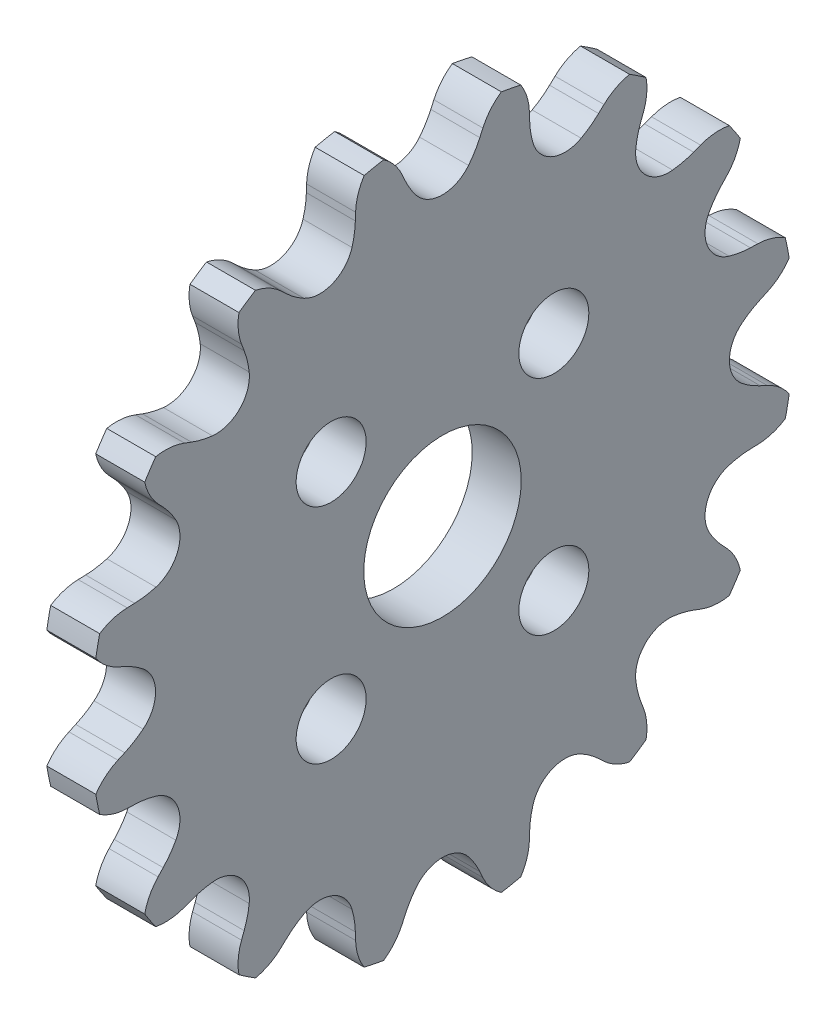
SolidWorks part; units mm, degrees
ref_plane "Front Plane" through (0, 0, 0) normal (0, 0, 1) x (1, 0, 0)
ref_plane "Top Plane" through (0, 0, 0) normal (0, 1, 0) x (1, 0, 0)
ref_plane "Right Plane" through (0, 0, 0) normal (1, 0, 0) x (0, 0, -1)
ref_plane "Plane1" through (0, 0, 0) normal (-1, 0, 0) x (0, -1, 0)
sketch "Sketch1" plane through (0, 0, 0) normal (-1, 0, 0) x (0, -1, 0)
  line L0 (-15.6424, 4.4271) -> (-16.0207, 4.4156)
  line L1 (-16.491, 2.0514) -> (-16.1459, 1.896)
  line L2 (-16.1459, -1.896) -> (-16.491, -2.0514)
  line L3 (-16.0207, -4.4156) -> (-15.6424, -4.4271)
  line L4 (-14.1913, -7.9304) -> (-14.4506, -8.2061)
  line L5 (-13.1114, -10.2103) -> (-12.7575, -10.0762)
  line L6 (-10.0762, -12.7575) -> (-10.2103, -13.1114)
  line L7 (-8.2061, -14.4506) -> (-7.9304, -14.1913)
  line L8 (-4.4271, -15.6424) -> (-4.4156, -16.0207)
  line L9 (-2.0514, -16.491) -> (-1.896, -16.1459)
  line L10 (1.896, -16.1459) -> (2.0514, -16.491)
  line L11 (4.4156, -16.0207) -> (4.4271, -15.6424)
  line L12 (7.9304, -14.1913) -> (8.2061, -14.4506)
  line L13 (10.2103, -13.1114) -> (10.0762, -12.7575)
  line L14 (12.7575, -10.0762) -> (13.1114, -10.2103)
  line L15 (14.4506, -8.2061) -> (14.1913, -7.9304)
  line L16 (15.6424, -4.4271) -> (16.0207, -4.4156)
  line L17 (16.491, -2.0514) -> (16.1459, -1.896)
  line L18 (16.1459, 1.896) -> (16.491, 2.0514)
  line L19 (16.0207, 4.4156) -> (15.6424, 4.4271)
  line L20 (14.1913, 7.9304) -> (14.4506, 8.2061)
  line L21 (13.1114, 10.2103) -> (12.7575, 10.0762)
  line L22 (10.0762, 12.7575) -> (10.2103, 13.1114)
  line L23 (8.2061, 14.4506) -> (7.9304, 14.1913)
  line L24 (4.4271, 15.6424) -> (4.4156, 16.0207)
  line L25 (2.0514, 16.491) -> (1.896, 16.1459)
  line L26 (-1.896, 16.1459) -> (-2.0514, 16.491)
  line L27 (-4.4156, 16.0207) -> (-4.4271, 15.6424)
  line L28 (-7.9304, 14.1913) -> (-8.2061, 14.4506)
  line L29 (-10.2103, 13.1114) -> (-10.0762, 12.7575)
  line L30 (-12.7575, 10.0762) -> (-13.1114, 10.2103)
  line L31 (-14.4506, 8.2061) -> (-14.1913, 7.9304)
  arc A0 (-13.5476, 7.0444) -> (-14.5607, 4.5984) centre (-15.0357, 6.228) cw
  arc A1 (-14.5607, 4.5984) -> (-15.6424, 4.4271) centre (-15.7749, 8.7641) cw
  arc A2 (-16.0207, 4.4156) -> (-17.4181, 3.9791) centre (-15.9376, 1.694) ccw
  arc A3 (-17.4181, 3.9791) -> (-17.6149, 2.9894) centre (0, 0) ccw
  arc A4 (-17.6149, 2.9894) -> (-16.491, 2.0514) centre (-15.3726, 4.534) ccw
  arc A5 (-16.1459, 1.896) -> (-15.2121, 1.3237) centre (-17.928, -2.0601) cw
  arc A6 (-15.2121, 1.3237) -> (-15.2121, -1.3237) centre (-16.2745, 0) cw
  arc A7 (-15.2121, -1.3237) -> (-16.1459, -1.896) centre (-17.928, 2.0601) cw
  arc A8 (-16.491, -2.0514) -> (-17.6149, -2.9894) centre (-15.3726, -4.534) ccw
  arc A9 (-17.6149, -2.9894) -> (-17.4181, -3.9791) centre (0, 0) ccw
  arc A10 (-17.4181, -3.9791) -> (-16.0207, -4.4156) centre (-15.9376, -1.694) ccw
  arc A11 (-15.6424, -4.4271) -> (-14.5607, -4.5984) centre (-15.7749, -8.7641) cw
  arc A12 (-14.5607, -4.5984) -> (-13.5476, -7.0444) centre (-15.0357, -6.228) cw
  arc A13 (-13.5476, -7.0444) -> (-14.1913, -7.9304) centre (-17.3517, -4.9574) cw
  arc A14 (-14.4506, -8.2061) -> (-15.1301, -9.5028) centre (-12.4674, -10.0717) ccw
  arc A15 (-15.1301, -9.5028) -> (-14.5694, -10.3419) centre (0, 0) ccw
  arc A16 (-14.5694, -10.3419) -> (-13.1114, -10.2103) centre (-14.0761, -7.6641) ccw
  arc A17 (-12.7575, -10.0762) -> (-11.6926, -9.8206) centre (-11.2202, -14.1337) cw
  arc A18 (-11.6926, -9.8206) -> (-9.8206, -11.6926) centre (-11.5078, -11.5078) cw
  arc A19 (-9.8206, -11.6926) -> (-10.0762, -12.7575) centre (-14.1337, -11.2202) cw
  arc A20 (-10.2103, -13.1114) -> (-10.3419, -14.5694) centre (-7.6641, -14.0761) ccw
  arc A21 (-10.3419, -14.5694) -> (-9.5028, -15.1301) centre (0, 0) ccw
  arc A22 (-9.5028, -15.1301) -> (-8.2061, -14.4506) centre (-10.0717, -12.4674) ccw
  arc A23 (-7.9304, -14.1913) -> (-7.0444, -13.5476) centre (-4.9574, -17.3517) cw
  arc A24 (-7.0444, -13.5476) -> (-4.5984, -14.5607) centre (-6.228, -15.0357) cw
  arc A25 (-4.5984, -14.5607) -> (-4.4271, -15.6424) centre (-8.7641, -15.7749) cw
  arc A26 (-4.4156, -16.0207) -> (-3.9791, -17.4181) centre (-1.694, -15.9376) ccw
  arc A27 (-3.9791, -17.4181) -> (-2.9894, -17.6149) centre (0, 0) ccw
  arc A28 (-2.9894, -17.6149) -> (-2.0514, -16.491) centre (-4.534, -15.3726) ccw
  arc A29 (-1.896, -16.1459) -> (-1.3237, -15.2121) centre (2.0601, -17.928) cw
  arc A30 (-1.3237, -15.2121) -> (1.3237, -15.2121) centre (0, -16.2745) cw
  arc A31 (1.3237, -15.2121) -> (1.896, -16.1459) centre (-2.0601, -17.928) cw
  arc A32 (2.0514, -16.491) -> (2.9894, -17.6149) centre (4.534, -15.3726) ccw
  arc A33 (2.9894, -17.6149) -> (3.9791, -17.4181) centre (0, 0) ccw
  arc A34 (3.9791, -17.4181) -> (4.4156, -16.0207) centre (1.694, -15.9376) ccw
  arc A35 (4.4271, -15.6424) -> (4.5984, -14.5607) centre (8.7641, -15.7749) cw
  arc A36 (4.5984, -14.5607) -> (7.0444, -13.5476) centre (6.228, -15.0357) cw
  arc A37 (7.0444, -13.5476) -> (7.9304, -14.1913) centre (4.9574, -17.3517) cw
  arc A38 (8.2061, -14.4506) -> (9.5028, -15.1301) centre (10.0717, -12.4674) ccw
  arc A39 (9.5028, -15.1301) -> (10.3419, -14.5694) centre (0, 0) ccw
  arc A40 (10.3419, -14.5694) -> (10.2103, -13.1114) centre (7.6641, -14.0761) ccw
  arc A41 (10.0762, -12.7575) -> (9.8206, -11.6926) centre (14.1337, -11.2202) cw
  arc A42 (9.8206, -11.6926) -> (11.6926, -9.8206) centre (11.5078, -11.5078) cw
  arc A43 (11.6926, -9.8206) -> (12.7575, -10.0762) centre (11.2202, -14.1337) cw
  arc A44 (13.1114, -10.2103) -> (14.5694, -10.3419) centre (14.0761, -7.6641) ccw
  arc A45 (14.5694, -10.3419) -> (15.1301, -9.5028) centre (0, 0) ccw
  arc A46 (15.1301, -9.5028) -> (14.4506, -8.2061) centre (12.4674, -10.0717) ccw
  arc A47 (14.1913, -7.9304) -> (13.5476, -7.0444) centre (17.3517, -4.9574) cw
  arc A48 (13.5476, -7.0444) -> (14.5607, -4.5984) centre (15.0357, -6.228) cw
  arc A49 (14.5607, -4.5984) -> (15.6424, -4.4271) centre (15.7749, -8.7641) cw
  arc A50 (16.0207, -4.4156) -> (17.4181, -3.9791) centre (15.9376, -1.694) ccw
  arc A51 (17.4181, -3.9791) -> (17.6149, -2.9894) centre (0, 0) ccw
  arc A52 (17.6149, -2.9894) -> (16.491, -2.0514) centre (15.3726, -4.534) ccw
  arc A53 (16.1459, -1.896) -> (15.2121, -1.3237) centre (17.928, 2.0601) cw
  arc A54 (15.2121, -1.3237) -> (15.2121, 1.3237) centre (16.2745, 0) cw
  arc A55 (15.2121, 1.3237) -> (16.1459, 1.896) centre (17.928, -2.0601) cw
  arc A56 (16.491, 2.0514) -> (17.6149, 2.9894) centre (15.3726, 4.534) ccw
  arc A57 (17.6149, 2.9894) -> (17.4181, 3.9791) centre (0, 0) ccw
  arc A58 (17.4181, 3.9791) -> (16.0207, 4.4156) centre (15.9376, 1.694) ccw
  arc A59 (15.6424, 4.4271) -> (14.5607, 4.5984) centre (15.7749, 8.7641) cw
  arc A60 (14.5607, 4.5984) -> (13.5476, 7.0444) centre (15.0357, 6.228) cw
  arc A61 (13.5476, 7.0444) -> (14.1913, 7.9304) centre (17.3517, 4.9574) cw
  arc A62 (14.4506, 8.2061) -> (15.1301, 9.5028) centre (12.4674, 10.0717) ccw
  arc A63 (15.1301, 9.5028) -> (14.5694, 10.3419) centre (0, 0) ccw
  arc A64 (14.5694, 10.3419) -> (13.1114, 10.2103) centre (14.0761, 7.6641) ccw
  arc A65 (12.7575, 10.0762) -> (11.6926, 9.8206) centre (11.2202, 14.1337) cw
  arc A66 (11.6926, 9.8206) -> (9.8206, 11.6926) centre (11.5078, 11.5078) cw
  arc A67 (9.8206, 11.6926) -> (10.0762, 12.7575) centre (14.1337, 11.2202) cw
  arc A68 (10.2103, 13.1114) -> (10.3419, 14.5694) centre (7.6641, 14.0761) ccw
  arc A69 (10.3419, 14.5694) -> (9.5028, 15.1301) centre (0, 0) ccw
  arc A70 (9.5028, 15.1301) -> (8.2061, 14.4506) centre (10.0717, 12.4674) ccw
  arc A71 (7.9304, 14.1913) -> (7.0444, 13.5476) centre (4.9574, 17.3517) cw
  arc A72 (7.0444, 13.5476) -> (4.5984, 14.5607) centre (6.228, 15.0357) cw
  arc A73 (4.5984, 14.5607) -> (4.4271, 15.6424) centre (8.7641, 15.7749) cw
  arc A74 (4.4156, 16.0207) -> (3.9791, 17.4181) centre (1.694, 15.9376) ccw
  arc A75 (3.9791, 17.4181) -> (2.9894, 17.6149) centre (0, 0) ccw
  arc A76 (2.9894, 17.6149) -> (2.0514, 16.491) centre (4.534, 15.3726) ccw
  arc A77 (1.896, 16.1459) -> (1.3237, 15.2121) centre (-2.0601, 17.928) cw
  arc A78 (1.3237, 15.2121) -> (-1.3237, 15.2121) centre (0, 16.2745) cw
  arc A79 (-1.3237, 15.2121) -> (-1.896, 16.1459) centre (2.0601, 17.928) cw
  arc A80 (-2.0514, 16.491) -> (-2.9894, 17.6149) centre (-4.534, 15.3726) ccw
  arc A81 (-2.9894, 17.6149) -> (-3.9791, 17.4181) centre (0, 0) ccw
  arc A82 (-3.9791, 17.4181) -> (-4.4156, 16.0207) centre (-1.694, 15.9376) ccw
  arc A83 (-4.4271, 15.6424) -> (-4.5984, 14.5607) centre (-8.7641, 15.7749) cw
  arc A84 (-4.5984, 14.5607) -> (-7.0444, 13.5476) centre (-6.228, 15.0357) cw
  arc A85 (-7.0444, 13.5476) -> (-7.9304, 14.1913) centre (-4.9574, 17.3517) cw
  arc A86 (-8.2061, 14.4506) -> (-9.5028, 15.1301) centre (-10.0717, 12.4674) ccw
  arc A87 (-9.5028, 15.1301) -> (-10.3419, 14.5694) centre (0, 0) ccw
  arc A88 (-10.3419, 14.5694) -> (-10.2103, 13.1114) centre (-7.6641, 14.0761) ccw
  arc A89 (-10.0762, 12.7575) -> (-9.8206, 11.6926) centre (-14.1337, 11.2202) cw
  arc A90 (-9.8206, 11.6926) -> (-11.6926, 9.8206) centre (-11.5078, 11.5078) cw
  arc A91 (-11.6926, 9.8206) -> (-12.7575, 10.0762) centre (-11.2202, 14.1337) cw
  arc A92 (-13.1114, 10.2103) -> (-14.5694, 10.3419) centre (-14.0761, 7.6641) ccw
  arc A93 (-14.5694, 10.3419) -> (-15.1301, 9.5028) centre (0, 0) ccw
  arc A94 (-15.1301, 9.5028) -> (-14.4506, 8.2061) centre (-12.4674, 10.0717) ccw
  arc A95 (-14.1913, 7.9304) -> (-13.5476, 7.0444) centre (-17.3517, 4.9574) cw
  circle A96 centre (0, 0) radius 4
  circle A97 centre (-5.6569, -5.6569) radius 1.778
  circle A98 centre (-5.6569, 5.6569) radius 1.778
  circle A99 centre (5.6569, 5.6569) radius 1.778
  circle A100 centre (5.6569, -5.6569) radius 1.778
extrude "Boss-Extrude1" add sketch "Sketch1" against normal blind 2.4892
